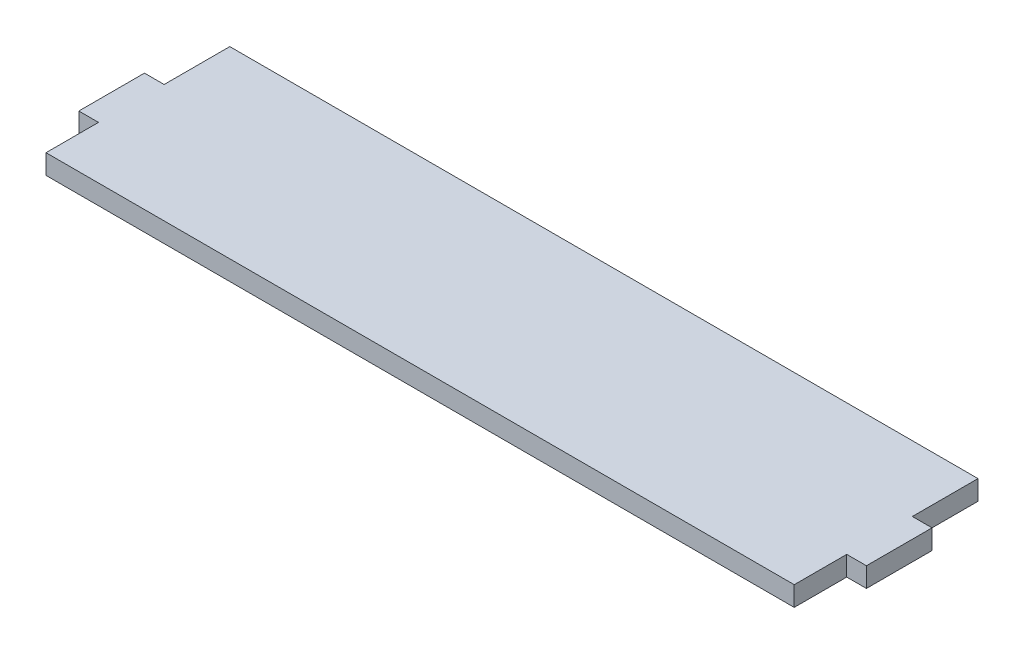
SolidWorks part; units mm, degrees
ref_plane "Alzado" through (0, 0, 0) normal (0, 0, 1) x (1, 0, 0)
ref_plane "Planta" through (0, 0, 0) normal (0, 1, 0) x (1, 0, 0)
ref_plane "Vista lateral" through (0, 0, 0) normal (1, 0, 0) x (0, 0, -1)
sketch "Croquis1" plane through (0, 0, 0) normal (0, 1, 0) x (1, 0, 0)
  line L0 (-57, 4) -> (-60, 4)
  line L1 (57, -14) -> (-57, -14)
  line L2 (57, -14) -> (57, -6)
  line L3 (57, 14) -> (-57, 14)
  line L4 (-57, -14) -> (-57, -6)
  line L5 (57, -14) -> (-57, 14) construction
  line L6 (57, 14) -> (-57, -14) construction
  line L7 (-60, 4) -> (-60, -6)
  line L8 (-60, -6) -> (-57, -6)
  line L9 (0, 0) -> (0, -37.7451) construction
  line L10 (60, -6) -> (57, -6)
  line L11 (60, 4) -> (60, -6)
  line L12 (57, 4) -> (60, 4)
  line L14 (-57, 4) -> (-57, 14)
  line L15 (57, 4) -> (57, 14)
  point P0 (0, 0)
  point P16 (-54.427, 15)
  dimension "D1" = 120
  dimension "35" = 28
  dimension "D3" = 10
  dimension "D4" = 3
  dimension "D5" = 10
extrude "Saliente-Extruir1" add sketch "Croquis1" along normal blind 3
